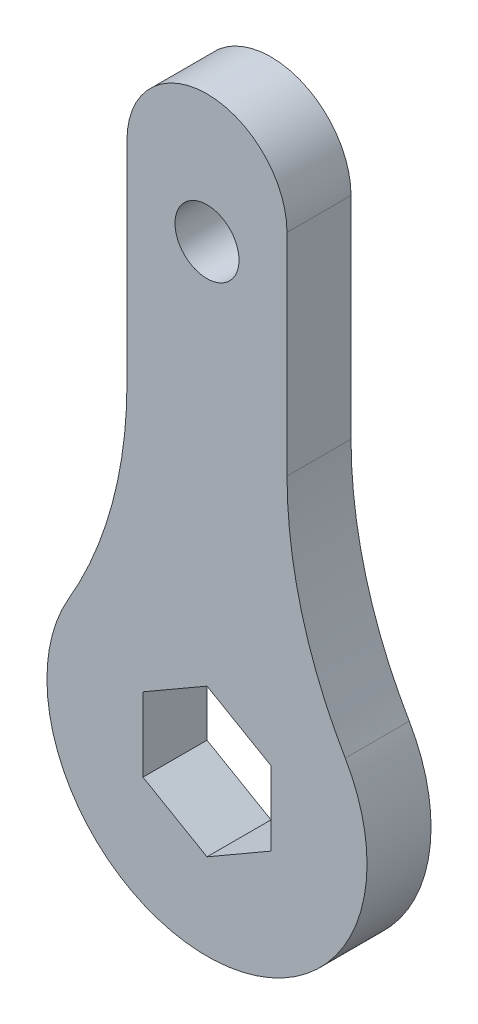
SolidWorks part; units mm, degrees
material "ABS"
ref_plane "Front" through (0, 0, 0) normal (0, 0, 1) x (1, 0, 0)
ref_plane "Top" through (0, 0, 0) normal (0, 1, 0) x (1, 0, 0)
ref_plane "Right" through (0, 0, 0) normal (1, 0, 0) x (0, 0, -1)
sketch "Sketch1" plane through (0, 0, 0) normal (0, 0, 1) x (1, 0, 0)
  line L1 (0, 3.4641) -> (-3, 1.7321)
  line L2 (-3, 1.7321) -> (-3, -1.7321)
  line L3 (-3, -1.7321) -> (0, -3.4641)
  line L4 (0, -3.4641) -> (3, -1.7321)
  line L5 (3, -1.7321) -> (3, 1.7321)
  line L6 (3, 1.7321) -> (0, 3.4641)
  line L8 (-3.75, 13.8632) -> (-3.75, 23.75)
  line L10 (3.75, 13.8632) -> (3.75, 23.75)
  arc A0 (-6.4773, 3.7809) -> (6.4773, 3.7809) centre (0, 0) ccw
  circle A1 centre (0, 0) radius 3 construction
  arc A2 (-3.75, 23.75) -> (3.75, 23.75) centre (0, 23.75) cw
  arc A3 (3.75, 13.8632) -> (6.4773, 3.7809) centre (23.75, 13.8632) ccw
  arc A4 (-3.75, 13.8632) -> (-6.4773, 3.7809) centre (-23.75, 13.8632) cw
  point P19 (0, 27.5)
  point P20 (0, -7.5)
  dimension "D2" = 20
  dimension "D3" = 7.5
  dimension "D5" = 35
  dimension "D1" = 6
  dimension "D4" = 7.5
extrude "Boss-Extrude1" add sketch "Sketch1" along normal blind 3
sketch "Sketch3" plane through (0, 0, 3) normal (0, 0, 1) x (1, 0, 0)
  circle A0 centre (0, 21.5) radius 1.5
  arc A1 (3.75, 23.75) -> (-3.75, 23.75) centre (0, 23.75) ccw construction
  dimension "D2" = 3
  dimension "D1" = 6
extrude "Cut-Extrude1" cut sketch "Sketch3" against normal blind 10
